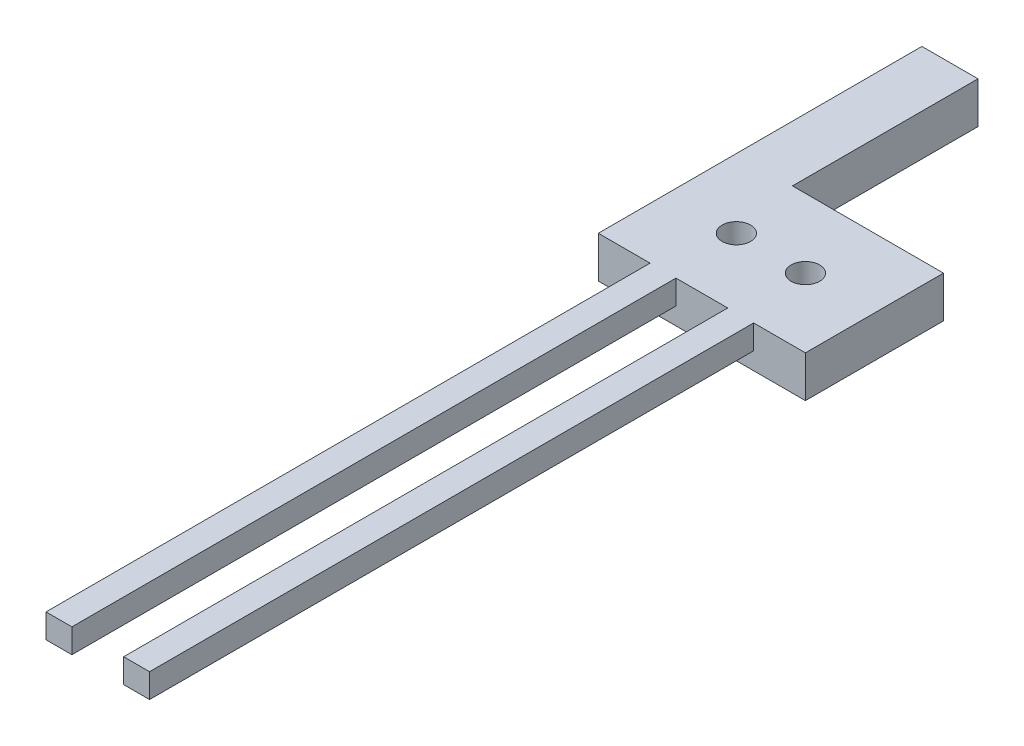
SolidWorks part; units mm, degrees
ref_plane "Front Plane" through (0, 0, 0) normal (0, 0, 1) x (1, 0, 0)
ref_plane "Top Plane" through (0, 0, 0) normal (0, 1, 0) x (1, 0, 0)
ref_plane "Right Plane" through (0, 0, 0) normal (1, 0, 0) x (0, 0, -1)
sketch "Sketch1" plane through (0, 0, 0) normal (0, -1, 0) x (1, 0, 0)
  line L0 (0, -8) -> (8, -8) construction
  line L1 (0, 0) -> (24, 0)
  line L2 (0, 0) -> (0, -16)
  line L3 (0, -16) -> (24, -16)
  line L4 (24, 0) -> (24, -16)
  line L5 (8, -8) -> (16, -8) construction
  line L6 (16, -8) -> (24, -8) construction
  circle A0 centre (8, -8) radius 1.65
  circle A1 centre (16, -8) radius 1.65
  dimension "D3" = 3.3
  dimension "D1" = 16
  dimension "D2" = 24
extrude "Boss-Extrude1" add sketch "Sketch1" along normal blind 4.8
sketch "Sketch2" plane through (0, 0, 0) normal (0, 0, 1) x (1, 0, 0)
  line L0 (24, 0) -> (0, 0) construction
  line L1 (6, 0) -> (9, 0)
  line L2 (6, 0) -> (6, -2.8)
  line L3 (6, -2.8) -> (9, -2.8)
  line L4 (9, 0) -> (9, -2.8)
  line L5 (0, 0) -> (6, 0) construction
  line L6 (15, 0) -> (18, 0)
  line L7 (15, 0) -> (15, -2.8)
  line L8 (15, -2.8) -> (18, -2.8)
  line L9 (18, 0) -> (18, -2.8)
  line L10 (9, 0) -> (15, 0) construction
  line L11 (18, 0) -> (24, 0) construction
  dimension "D1" = 2.8
  dimension "D2" = 3
  dimension "D3" = 3
extrude "Boss-Extrude2" add sketch "Sketch2" along normal blind 70
sketch "Sketch3" plane through (0, 0, 0) normal (0, 1, 0) x (1, 0, 0)
  circle A0 centre (8, 8) radius 2.85
  circle A1 centre (16, 8) radius 2.85
  dimension "D1" = 5.7
extrude "Cut-Extrude1" [suppressed] cut sketch "Sketch3" against normal blind 3.3
sketch "Sketch4" plane through (0, 0, 0) normal (0, 1, 0) x (1, 0, 0)
  line L0 (6.5, 37.5) -> (0, 37.5)
  line L1 (0, 37.5) -> (0, 16)
  line L2 (0, 16) -> (6.5, 16)
  line L3 (0, 16) -> (24, 16) construction
  line L4 (6.5, 16) -> (6.5, 37.5)
extrude "Boss-Extrude3" add sketch "Sketch4" against normal blind 4.8
